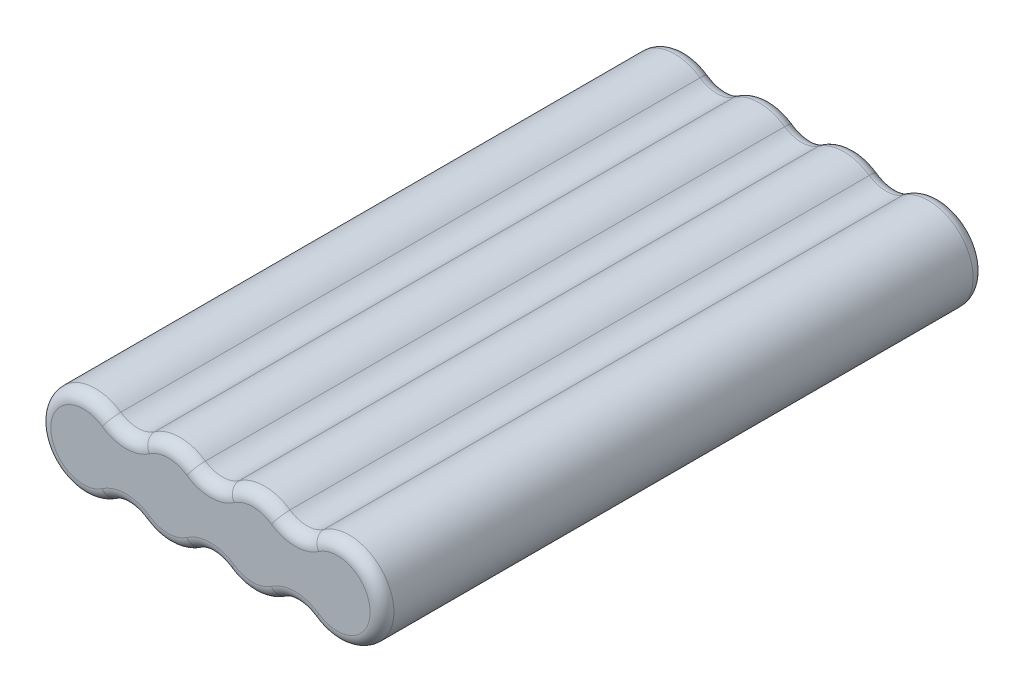
SolidWorks part; units mm, degrees
ref_plane "Front Plane" through (0, 0, 0) normal (0, 0, 1) x (1, 0, 0)
ref_plane "Top Plane" through (0, 0, 0) normal (0, 1, 0) x (1, 0, 0)
ref_plane "Right Plane" through (0, 0, 0) normal (1, 0, 0) x (0, 0, -1)
sketch "Sketch1" plane through (0, 0, 0) normal (0, 0, 1) x (1, 0, 0)
  line L0 (-21.329, 0) -> (-7.1097, 0) construction
  line L1 (-7.1097, 0) -> (7.1097, 0) construction
  line L2 (7.1097, 0) -> (21.329, 0) construction
  arc A0 (-17.0632, 6.1687) -> (-17.0632, -6.1687) centre (-21.329, 0) ccw
  arc A1 (-11.3755, -6.1687) -> (-2.8439, -6.1687) centre (-7.1097, 0) ccw
  arc A2 (2.8439, -6.1687) -> (11.3755, -6.1687) centre (7.1097, 0) ccw
  arc A3 (17.0632, -6.1687) -> (17.0632, 6.1687) centre (21.329, 0) ccw
  arc A4 (-2.8439, 6.1687) -> (-11.3755, 6.1687) centre (-7.1097, 0) ccw
  arc A5 (11.3755, 6.1687) -> (2.8439, 6.1687) centre (7.1097, 0) ccw
  arc A6 (17.0632, -6.1687) -> (11.3755, -6.1687) centre (14.2193, -10.2812) ccw
  arc A7 (2.8439, -6.1687) -> (-2.8439, -6.1687) centre (0, -10.2812) ccw
  arc A8 (-11.3755, -6.1687) -> (-17.0632, -6.1687) centre (-14.2193, -10.2812) ccw
  arc A9 (11.3755, 6.1687) -> (17.0632, 6.1687) centre (14.2193, 10.2812) ccw
  arc A10 (-2.8439, 6.1687) -> (2.8439, 6.1687) centre (0, 10.2812) ccw
  arc A11 (-11.3755, 6.1687) -> (-17.0632, 6.1687) centre (-14.2193, 10.2812) cw
  point P8 (-28.829, 0)
  point P9 (28.829, 0)
  dimension "D1" = 15
  dimension "D3" = 5
  dimension "D2" = 57.658
extrude "Boss-Extrude1" add sketch "Sketch1" along normal mid plane 101.346
fillet "Fillet1" radius 2 24 edges at (28.829, 0, -50.673) (14.2193, 5.2812, -50.673) (7.1097, 7.5, -50.673) (0, 5.2812, -50.673) (-7.1097, 7.5, -50.673) (-14.2193, 5.2812, -50.673) (-28.829, 0, -50.673) (-14.2193, -5.2812, -50.673) (-7.1097, -7.5, -50.673) (0, -5.2812, -50.673) (7.1097, -7.5, -50.673) (14.2193, -5.2812, -50.673) (7.1097, -7.5, 50.673) (0, -5.2812, 50.673) (-7.1097, -7.5, 50.673) (-14.2193, -5.2812, 50.673) (-28.829, 0, 50.673) (-14.2193, 5.2812, 50.673) (-7.1097, 7.5, 50.673) (0, 5.2812, 50.673) (7.1097, 7.5, 50.673) (14.2193, 5.2812, 50.673) (28.829, 0, 50.673) (14.2193, -5.2812, 50.673)
ref_plane "Plane1" through (0, 0, 0) normal (0, 1, 0) x (1, 0, 0)
